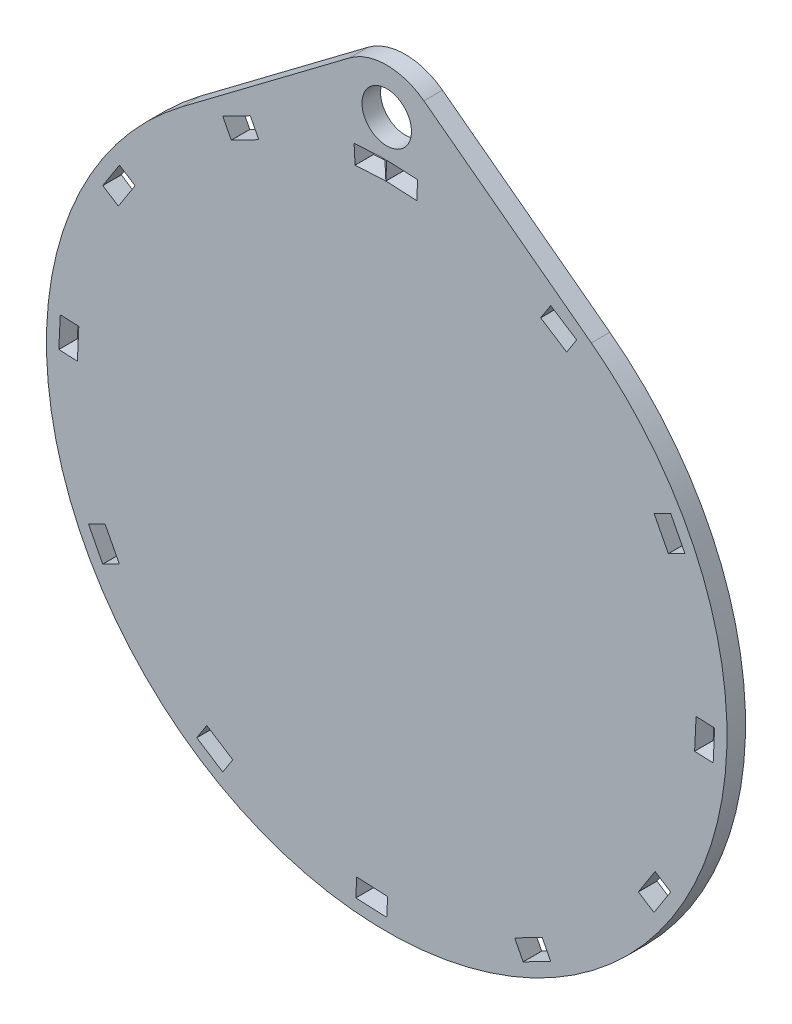
SolidWorks part; units mm, degrees
ref_plane "Front" through (0, 0, 0) normal (0, 0, 1) x (1, 0, 0)
ref_plane "Top" through (0, 0, 0) normal (0, 1, 0) x (1, 0, 0)
ref_plane "Right" through (0, 0, 0) normal (1, 0, 0) x (0, 0, -1)
sketch "Sketch1" plane through (0, 0, 0) normal (0, 0, 1) x (1, 0, 0)
  line L0 (52.9995, -0.0099) -> (52.7646, -4.9844)
  line L1 (52.7542, -4.9939) -> (49.7775, -4.8534)
  line L2 (52.99, 0.0005) -> (50.0133, 0.1411)
  line L3 (50.0029, 0.1316) -> (49.768, -4.8429)
  line L4 (-0.2989, 52.9892) -> (-0.142, 50.0133)
  line L5 (43.1895, -30.7019) -> (40.6819, -29.0919)
  line L6 (43.3695, -24.8875) -> (40.6789, -29.078)
  line L7 (45.8909, -26.4946) -> (43.3833, -24.8845)
  line L8 (45.8939, -26.5084) -> (43.2033, -30.6989)
  line L9 (22.0522, -48.1834) -> (20.6856, -45.5352)
  line L10 (25.1153, -43.238) -> (20.6899, -45.5217)
  line L11 (26.4954, -45.8904) -> (25.1288, -43.2423)
  line L12 (26.4911, -45.9039) -> (22.0657, -48.1877)
  line L13 (-4.994, -52.7541) -> (-4.8534, -49.7774)
  line L14 (0.1315, -50.0028) -> (-4.8429, -49.7679)
  line L15 (0.0005, -52.99) -> (0.141, -50.0133)
  line L16 (-0.01, -52.9995) -> (-4.9844, -52.7646)
  line L17 (-30.702, -43.1894) -> (-29.0919, -40.6818)
  line L18 (-24.8875, -43.3695) -> (-29.0781, -40.6788)
  line L19 (-26.4946, -45.8909) -> (-24.8845, -43.3833)
  line L20 (-26.5084, -45.8939) -> (-30.699, -43.2032)
  line L21 (-48.1834, -22.0521) -> (-45.5353, -20.6855)
  line L22 (-43.238, -25.1153) -> (-45.5218, -20.6898)
  line L23 (-45.8905, -26.4954) -> (-43.2423, -25.1288)
  line L24 (-45.9039, -26.4911) -> (-48.1877, -22.0656)
  line L25 (-52.7542, 4.994) -> (-49.7775, 4.8534)
  line L26 (-50.0029, -0.1315) -> (-49.768, 4.843)
  line L27 (-52.99, -0.0004) -> (-50.0133, -0.141)
  line L28 (-52.9995, 0.01) -> (-52.7646, 4.9845)
  line L29 (-43.1895, 30.702) -> (-40.6819, 29.0919)
  line L30 (-43.3695, 24.8876) -> (-40.6788, 29.0781)
  line L31 (-45.8909, 26.4946) -> (-43.3833, 24.8846)
  line L32 (-45.8939, 26.5085) -> (-43.2033, 30.699)
  line L33 (-22.0522, 48.1835) -> (-20.6856, 45.5353)
  line L34 (-25.1153, 43.238) -> (-20.6899, 45.5218)
  line L35 (-26.4954, 45.8905) -> (-25.1288, 43.2423)
  line L36 (-26.4911, 45.904) -> (-22.0657, 48.1878)
  line L37 (4.994, 52.7542) -> (4.8534, 49.7775)
  line L38 (-0.1315, 50.0029) -> (4.8429, 49.768)
  line L39 (-0.0005, 52.9901) -> (-0.141, 50.0134)
  line L40 (0.01, 52.9996) -> (4.9844, 52.7647)
  line L41 (30.702, 43.1895) -> (29.0919, 40.6819)
  line L42 (24.8875, 43.3696) -> (29.0781, 40.6789)
  line L43 (26.4946, 45.891) -> (24.8845, 43.3834)
  line L44 (26.5084, 45.894) -> (30.699, 43.2033)
  line L45 (48.1834, 22.0522) -> (45.5353, 20.6856)
  line L46 (43.238, 25.1154) -> (45.5218, 20.6899)
  line L47 (45.8905, 26.4955) -> (43.2423, 25.1288)
  line L48 (45.9039, 26.4912) -> (48.1877, 22.0657)
  line L49 (-33.0691, 43.9481) -> (-6.0126, 64.307)
  line L50 (-5.1071, 49.7416) -> (-0.1515, 50.0028)
  line L51 (33.0691, 43.9481) -> (6.0126, 64.307)
  line L52 (-5.2745, 52.7269) -> (-5.1176, 49.751)
  line L53 (-5.2651, 52.7374) -> (-0.3094, 52.9987)
  arc A0 (-33.0691, 43.9481) -> (33.0691, 43.9481) centre (0, 0) ccw
  circle A1 centre (0, 59) radius 4
  arc A2 (6.0126, 64.307) -> (-6.0126, 64.307) centre (0, 56.3165) ccw
  arc A3 (-43.3833, 24.8846) -> (-43.3695, 24.8876) centre (-43.3779, 24.893) ccw
  arc A4 (-43.2033, 30.699) -> (-43.1895, 30.702) centre (-43.1949, 30.6936) cw
  arc A5 (-45.8939, 26.5085) -> (-45.8909, 26.4946) centre (-45.8855, 26.5031) ccw
  arc A6 (-43.3695, 24.8876) -> (-43.3833, 24.8846) centre (-43.3779, 24.893) cw
  arc A7 (-40.6788, 29.0781) -> (-40.6819, 29.0919) centre (-40.6873, 29.0835) ccw
  arc A8 (-25.1153, 43.238) -> (-25.1288, 43.2423) centre (-25.1199, 43.2469) cw
  arc A9 (-20.6856, 45.5353) -> (-20.6899, 45.5218) centre (-20.6945, 45.5307) cw
  arc A10 (-22.0522, 48.1835) -> (-22.0657, 48.1878) centre (-22.0611, 48.1789) ccw
  arc A11 (-26.4954, 45.8905) -> (-26.4911, 45.904) centre (-26.4865, 45.8951) cw
  arc A12 (-5.1071, 49.7416) -> (-5.1176, 49.751) centre (-5.1076, 49.7516) cw
  arc A13 (-0.1315, 50.0029) -> (-0.141, 50.0134) centre (-0.131, 50.0129) cw
  arc A14 (4.8534, 49.7775) -> (4.8429, 49.768) centre (4.8434, 49.778) cw
  arc A15 (4.994, 52.7542) -> (4.9844, 52.7647) centre (4.984, 52.7547) ccw
  arc A16 (-0.0005, 52.9901) -> (0.01, 52.9996) centre (0.0095, 52.9896) cw
  arc A17 (-0.142, 50.0133) -> (-0.1515, 50.0028) centre (-0.152, 50.0128) cw
  arc A18 (-0.2989, 52.9892) -> (-0.3094, 52.9987) centre (-0.3089, 52.9887) ccw
  arc A19 (-5.2745, 52.7269) -> (-5.2651, 52.7374) centre (-5.2645, 52.7274) cw
  arc A20 (24.8875, 43.3696) -> (24.8845, 43.3834) centre (24.8929, 43.378) cw
  arc A21 (29.0919, 40.6819) -> (29.0781, 40.6789) centre (29.0835, 40.6873) cw
  arc A22 (30.702, 43.1895) -> (30.699, 43.2033) centre (30.6936, 43.1949) ccw
  arc A23 (26.4946, 45.891) -> (26.5084, 45.894) centre (26.503, 45.8856) cw
  arc A24 (-50.0029, -0.1315) -> (-50.0133, -0.141) centre (-50.0129, -0.131) cw
  arc A25 (-49.7775, 4.8534) -> (-49.768, 4.843) centre (-49.7779, 4.8434) cw
  arc A26 (-52.7542, 4.994) -> (-52.7646, 4.9845) centre (-52.7546, 4.984) ccw
  arc A27 (-52.99, -0.0004) -> (-52.9995, 0.01) centre (-52.9895, 0.0096) cw
  arc A28 (-43.238, -25.1153) -> (-43.2423, -25.1288) centre (-43.2469, -25.1199) cw
  arc A29 (-45.5353, -20.6855) -> (-45.5218, -20.6898) centre (-45.5307, -20.6944) cw
  arc A30 (-48.1834, -22.0521) -> (-48.1877, -22.0656) centre (-48.1788, -22.061) ccw
  arc A31 (-45.8905, -26.4954) -> (-45.9039, -26.4911) centre (-45.895, -26.4865) cw
  arc A32 (-24.8875, -43.3695) -> (-24.8845, -43.3833) centre (-24.8929, -43.3779) cw
  arc A33 (-29.0919, -40.6818) -> (-29.0781, -40.6788) centre (-29.0835, -40.6872) cw
  arc A34 (-30.702, -43.1894) -> (-30.699, -43.2032) centre (-30.6936, -43.1948) ccw
  arc A35 (-26.4946, -45.8909) -> (-26.5084, -45.8939) centre (-26.503, -45.8855) cw
  arc A36 (0.1315, -50.0028) -> (0.141, -50.0133) centre (0.1311, -50.0128) cw
  arc A37 (-4.8534, -49.7774) -> (-4.8429, -49.7679) centre (-4.8434, -49.7779) cw
  arc A38 (-4.994, -52.7541) -> (-4.9844, -52.7646) centre (-4.984, -52.7546) ccw
  arc A39 (0.0005, -52.99) -> (-0.01, -52.9995) centre (-0.0095, -52.9895) cw
  arc A40 (25.1153, -43.238) -> (25.1288, -43.2423) centre (25.1199, -43.2468) cw
  arc A41 (20.6856, -45.5352) -> (20.6899, -45.5217) centre (20.6945, -45.5306) cw
  arc A42 (22.0522, -48.1834) -> (22.0657, -48.1877) centre (22.0611, -48.1788) ccw
  arc A43 (26.4954, -45.8904) -> (26.4911, -45.9039) centre (26.4865, -45.895) cw
  arc A44 (43.3695, -24.8875) -> (43.3833, -24.8845) centre (43.3779, -24.8929) cw
  arc A45 (40.6819, -29.0919) -> (40.6789, -29.078) centre (40.6873, -29.0834) cw
  arc A46 (43.1895, -30.7019) -> (43.2033, -30.6989) centre (43.1949, -30.6935) ccw
  arc A47 (45.8909, -26.4946) -> (45.8939, -26.5084) centre (45.8855, -26.503) cw
  arc A48 (50.0133, 0.1411) -> (50.0029, 0.1316) centre (50.0129, 0.1311) ccw
  arc A49 (49.7775, -4.8534) -> (49.768, -4.8429) centre (49.778, -4.8434) cw
  arc A50 (52.7646, -4.9844) -> (52.7542, -4.9939) centre (52.7546, -4.9839) cw
  arc A51 (52.9995, -0.0099) -> (52.99, 0.0005) centre (52.9895, -0.0095) ccw
  arc A52 (43.238, 25.1154) -> (43.2423, 25.1288) centre (43.2469, 25.12) cw
  arc A53 (45.5353, 20.6856) -> (45.5218, 20.6899) centre (45.5307, 20.6945) cw
  arc A54 (48.1834, 22.0522) -> (48.1877, 22.0657) centre (48.1788, 22.0611) ccw
  arc A55 (45.8905, 26.4955) -> (45.9039, 26.4912) centre (45.895, 26.4866) cw
  arc A56 (26.5084, 45.894) -> (26.4946, 45.891) centre (26.503, 45.8856) ccw
  arc A57 (24.8875, 43.3696) -> (24.8845, 43.3834) centre (24.8929, 43.378) cw
  arc A58 (29.0919, 40.6819) -> (29.0781, 40.6789) centre (29.0835, 40.6873) cw
  arc A59 (30.702, 43.1895) -> (30.699, 43.2033) centre (30.6936, 43.1949) ccw
  point P57 (0, 0)
  point P69 (-45.8993, 26.5)
  point P75 (-40.6734, 29.0865)
  point P82 (-22.0568, 48.1924)
  point P87 (-5.1171, 49.741)
  point P90 (-0.1415, 50.0034)
  point P99 (-0.1415, 50.0034)
  point P102 (-0.2995, 52.9992)
  point P105 (-5.275, 52.7369)
  point P140 (0.1415, -50.0033)
  point P151 (20.681, -45.5263)
  point P166 (50.0033, 0.1416)
  point P169 (49.7675, -4.8529)
  point P172 (52.7642, -4.9944)
  point P175 (53, 0)
  dimension "D1" = 110
  dimension "D2" = 52.941
  dimension "D3" = 5
  dimension "D12" = 59
  dimension "D14" = 8
  dimension "D15" = 10
  dimension "D24" = 0.01
  dimension "D25" = 0.01
  dimension "D26" = 0.01
  dimension "D27" = 0.01
  dimension "D28" = 0.01
  dimension "D29" = 0.01
  dimension "D30" = 0.01
  dimension "D31" = 0.01
  dimension "D32" = 0.01
  dimension "D33" = 0.01
  dimension "D34" = 0.01
  dimension "D35" = 0.01
  dimension "D36" = 0.01
  dimension "D37" = 0.01
  dimension "D38" = 0.01
  dimension "D39" = 0.01
  dimension "D40" = 0.01
  dimension "D41" = 0.01
  dimension "D4" = 90
  dimension "D5" = 3
  dimension "D6" = 3
  dimension "D7" = 90
  dimension "D9" = 99.882
  dimension "D10" = 21.0217
  dimension "D11" = 5.2259
  dimension "D13" = 90
  dimension "D16" = 90
  dimension "D17" = 3
  dimension "D18" = 3
  dimension "D19" = 0
  dimension "D20" = 53
  dimension "D21" = 56.3165
  dimension "D22" = 106.08
  dimension "D23" = 26.6477
  dimension "D8" = 12
extrude "Boss-Extrude2" add sketch "Sketch1" along normal blind 3 contours L51 A2 L49 A0 A51 L0 A50 L1 A49 L3 A48 L2 A7 L30 A3 L31 A5 L32 A4 L29 A1 L35 A11 L36 A10 L33 A9 L34 A8 L39 A16 L40 A15 L37 A14 L38 A13 L52 A19 L53 A18 L4 A17 L50 A12
